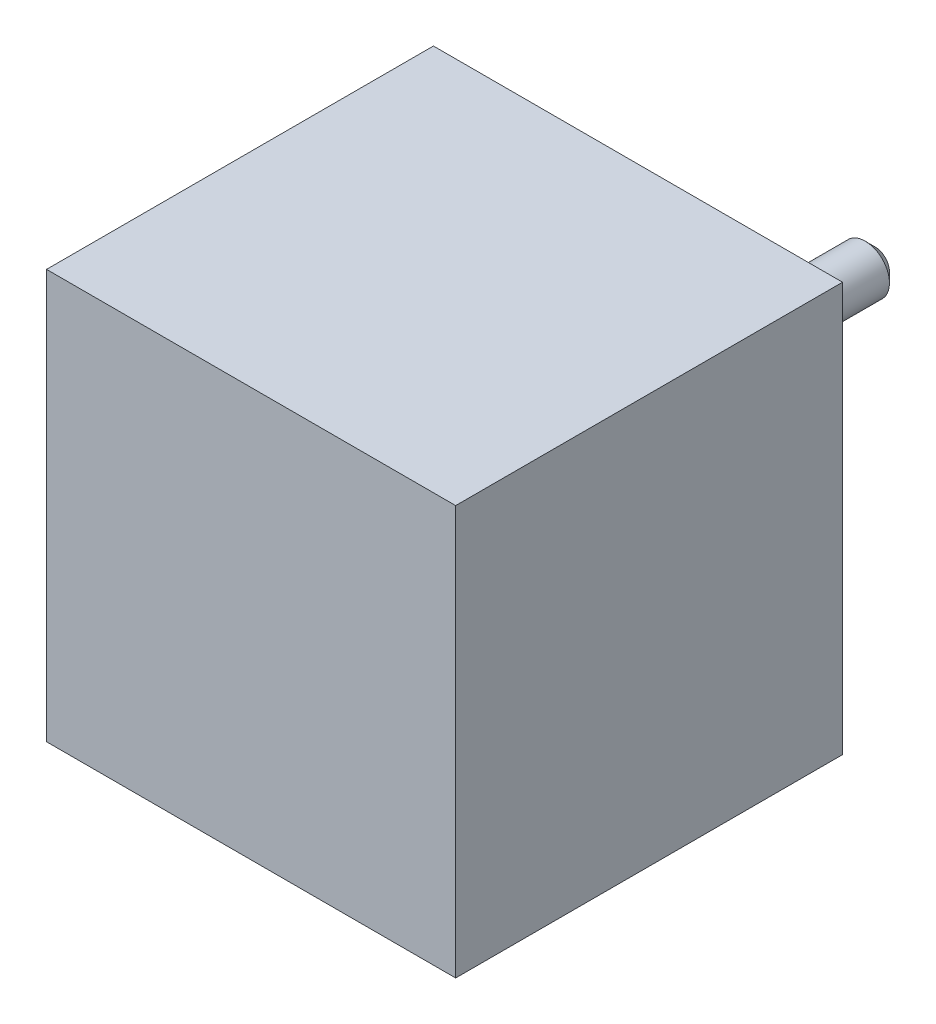
SolidWorks part; units mm, degrees
ref_plane "Ebene vorne" through (0, 0, 0) normal (0, 0, 1) x (1, 0, 0)
ref_plane "Ebene oben" through (0, 0, 0) normal (0, 1, 0) x (1, 0, 0)
ref_plane "Ebene rechts" through (0, 0, 0) normal (1, 0, 0) x (0, 0, -1)
sketch "Skizze1" plane through (0, 0, 0) normal (0, 0, 1) x (1, 0, 0)
  line L1 (0, 0) -> (42.3, 0)
  line L2 (0, 0) -> (0, 42.3)
  line L3 (0, 42.3) -> (42.3, 42.3)
  line L4 (42.3, 0) -> (42.3, 42.3)
  dimension "D1" = 42.3
  dimension "D2" = 42.3
extrude "Aufsatz-Linear austragen1" add sketch "Skizze1" along normal blind 40
sketch "Skizze2" plane through (0, 0, 0) normal (0, 0, -1) x (-1, 0, 0)
  line L0 (-42.3, 42.3) -> (0, 42.3) construction
  line L1 (0, 42.3) -> (0, 0) construction
  circle A0 centre (-21.15, 21.15) radius 11
  dimension "D1" = 22
  dimension "D2" = 21.15
  dimension "D3" = 21.15
extrude "Aufsatz-Linear austragen2" add sketch "Skizze2" along normal blind 2
sketch "Skizze3" plane through (0, 0, -2) normal (0, 0, -1) x (-1, 0, 0)
  line L2 (0, 42.3) -> (0, 0) construction
  line L3 (-42.3, 42.3) -> (0, 42.3) construction
  circle A0 centre (-21.15, 21.15) radius 2.5
  dimension "D1" = 5
  dimension "D2" = 21.15
  dimension "D3" = 21.15
extrude "Aufsatz-Linear austragen3" add sketch "Skizze3" along normal blind 22.5
chamfer "Fase1" distance 1 angle 45 1 edges at (18.65, 21.15, -24.5)
sketch "Skizze4" plane through (0, 0, 0) normal (0, 0, -1) x (-1, 0, 0)
  line L0 (-42.3, 0) -> (-42.3, 42.3) construction
  line L1 (-42.3, 42.3) -> (0, 42.3) construction
  line L2 (0, 0) -> (-42.3, 0) construction
  line L3 (0, 42.3) -> (0, 0) construction
  circle A0 centre (-5.65, 36.65) radius 1.25
  circle A1 centre (-5.65, 5.65) radius 1.25
  circle A2 centre (-36.65, 5.65) radius 1.25
  circle A3 centre (-36.65, 36.65) radius 1.25
  dimension "D1" = 2.5
  dimension "D2" = 2.5
  dimension "D3" = 2.5
  dimension "D4" = 2.5
  dimension "D7" = 5.65
  dimension "D5" = 5.65
  dimension "D6" = 5.65
  dimension "D8" = 5.65
  dimension "D9" = 5.65
  dimension "D10" = 5.65
  dimension "D11" = 5.65
  dimension "D12" = 5.65
extrude "Schnitt-Linear austragen1" cut sketch "Skizze4" against normal blind 4.5
cosmetic thread "Gewindedarstellung1" parameters "D1"=4.5, "D2"=3
cosmetic thread "Gewindedarstellung2" parameters "D1"=4.5, "D2"=3
cosmetic thread "Gewindedarstellung3" parameters "D1"=4.5, "D2"=3
cosmetic thread "Gewindedarstellung4" parameters "D1"=4.5, "D2"=3
